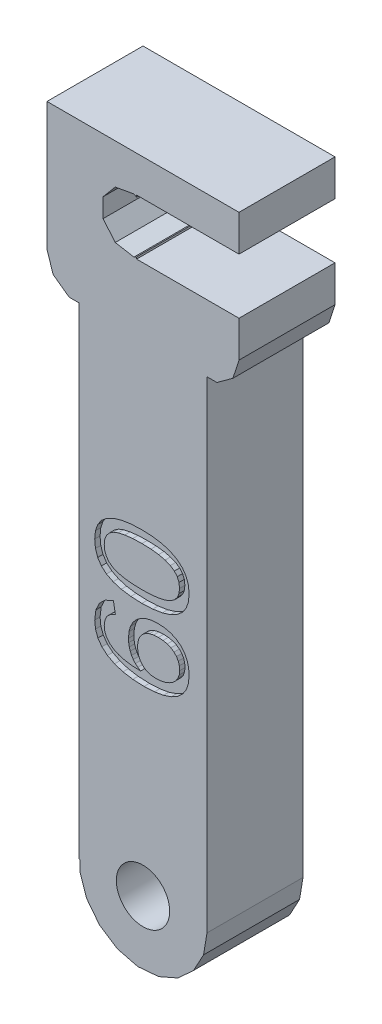
SolidWorks part; units mm, degrees
ref_plane "Front Plane" through (0, 0, 0) normal (0, 0, 1) x (1, 0, 0)
ref_plane "Top Plane" through (0, 0, 0) normal (0, 1, 0) x (1, 0, 0)
ref_plane "Right Plane" through (0, 0, 0) normal (1, 0, 0) x (0, 0, -1)
ref_plane "Plane1" through (0, 0, 4.5) normal (0, 0, 1) x (1, 0, 0)
sketch "Sketch1" plane through (0, 0, 4.5) normal (0, 0, 1) x (1, 0, 0)
  line L0 (8.427, 16.2366) -> (9, 18)
  line L1 (9, 18) -> (9, 30)
  line L2 (9, 30) -> (-9, 30)
  line L3 (-9, 30) -> (-9, 18)
  line L4 (-9, 18) -> (-8.427, 16.2366)
  line L5 (-8.427, 16.2366) -> (-6.9271, 15.1468)
  line L6 (-6.9271, 15.1468) -> (-6, 15.1468)
  line L7 (-6, 15.1468) -> (-6, -30)
  line L8 (-6, -30) -> (-5.9182, -30)
  line L9 (-5.9182, -30) -> (-5.9182, -30.9876)
  line L10 (-5.9182, -30.9876) -> (-5.2768, -32.8557)
  line L11 (-5.2768, -32.8557) -> (-4.0637, -34.4143)
  line L12 (-4.0637, -34.4143) -> (-2.4102, -35.4946)
  line L13 (-2.4102, -35.4946) -> (-0.4955, -35.9795)
  line L14 (-0.4955, -35.9795) -> (1.4729, -35.8164)
  line L15 (1.4729, -35.8164) -> (3.2817, -35.023)
  line L16 (3.2817, -35.023) -> (4.7348, -33.6853)
  line L17 (4.7348, -33.6853) -> (5.6749, -31.9482)
  line L18 (5.6749, -31.9482) -> (6, -30)
  line L19 (6, -30) -> (6, 15.1468)
  line L20 (6, 15.1468) -> (6.9271, 15.1468)
  line L21 (6.9271, 15.1468) -> (8.427, 16.2366)
extrude "Boss-Extrude1" add sketch "Sketch1" against normal blind 9
sketch "Sketch2" plane through (0, 0, -4.5) normal (0, 0, -1) x (-1, 0, 0)
  line L0 (-9, 26.6) -> (-9, 21.4)
  line L1 (-9, 21.4) -> (0.6, 21.4)
  line L2 (0.6, 21.4) -> (0.6, 21.583)
  line L3 (0.6, 21.583) -> (0.8485, 21.4395)
  line L4 (0.8485, 21.4395) -> (2.6, 21.7483)
  line L5 (2.6, 21.7483) -> (3.7432, 23.1107)
  line L6 (3.7432, 23.1107) -> (3.7432, 24.8893)
  line L7 (3.7432, 24.8893) -> (2.6, 26.2517)
  line L8 (2.6, 26.2517) -> (1.6624, 26.417)
  line L9 (1.6624, 26.417) -> (0.6, 26.417)
  line L10 (0.6, 26.417) -> (0.6, 26.6)
  line L11 (0.6, 26.6) -> (-9, 26.6)
extrude "Cut-Extrude1" cut sketch "Sketch2" against normal through all
sketch "Sketch3" plane through (0, 0, -4.5) normal (0, 0, -1) x (-1, 0, 0)
  line L0 (1.7678, -28.2322) -> (0, -27.5)
  line L1 (0, -27.5) -> (-1.7678, -28.2322)
  line L2 (-1.7678, -28.2322) -> (-2.5, -30)
  line L3 (-2.5, -30) -> (-1.7678, -31.7678)
  line L4 (-1.7678, -31.7678) -> (0, -32.5)
  line L5 (0, -32.5) -> (1.7678, -31.7678)
  line L6 (1.7678, -31.7678) -> (2.5, -30)
  line L7 (2.5, -30) -> (1.7678, -28.2322)
extrude "Cut-Extrude2" cut sketch "Sketch3" against normal through all
sketch "Sketch4" plane through (0, 0, 4.5) normal (0, 0, 1) x (1, 0, 0)
  line L0 (-2.5848, -8.4634) -> (-2.774, -7.4137)
  line L1 (-2.774, -7.4137) -> (-3.5403, -7.757)
  line L2 (-3.5403, -7.757) -> (-4.0877, -8.2803)
  line L3 (-4.0877, -8.2803) -> (-4.4161, -8.9837)
  line L4 (-4.4161, -8.9837) -> (-4.5256, -9.8672)
  line L5 (-4.5256, -9.8672) -> (-4.4508, -10.5633)
  line L6 (-4.4508, -10.5633) -> (-4.2265, -11.1748)
  line L7 (-4.2265, -11.1748) -> (-3.8527, -11.7015)
  line L8 (-3.8527, -11.7015) -> (-3.3293, -12.1436)
  line L9 (-3.3293, -12.1436) -> (-2.6664, -12.4934)
  line L10 (-2.6664, -12.4934) -> (-1.8738, -12.7432)
  line L11 (-1.8738, -12.7432) -> (-0.9514, -12.8931)
  line L12 (-0.9514, -12.8931) -> (0.1006, -12.9431)
  line L13 (0.1006, -12.9431) -> (1.0706, -12.895)
  line L14 (1.0706, -12.895) -> (1.9178, -12.7509)
  line L15 (1.9178, -12.7509) -> (2.6422, -12.5106)
  line L16 (2.6422, -12.5106) -> (3.2437, -12.1741)
  line L17 (3.2437, -12.1741) -> (3.7163, -11.7469)
  line L18 (3.7163, -11.7469) -> (4.0539, -11.2343)
  line L19 (4.0539, -11.2343) -> (4.2564, -10.6361)
  line L20 (4.2564, -10.6361) -> (4.3239, -9.9526)
  line L21 (4.3239, -9.9526) -> (4.2747, -9.3377)
  line L22 (4.2747, -9.3377) -> (4.1271, -8.793)
  line L23 (4.1271, -8.793) -> (3.8811, -8.3185)
  line L24 (3.8811, -8.3185) -> (3.5367, -7.9142)
  line L25 (3.5367, -7.9142) -> (3.1072, -7.5911)
  line L26 (3.1072, -7.5911) -> (2.6059, -7.3603)
  line L27 (2.6059, -7.3603) -> (2.033, -7.2219)
  line L28 (2.033, -7.2219) -> (1.3883, -7.1757)
  line L29 (1.3883, -7.1757) -> (0.7917, -7.2194)
  line L30 (0.7917, -7.2194) -> (0.2592, -7.3504)
  line L31 (0.2592, -7.3504) -> (-0.2092, -7.5688)
  line L32 (-0.2092, -7.5688) -> (-0.6135, -7.8746)
  line L33 (-0.6135, -7.8746) -> (-0.9392, -8.2547)
  line L34 (-0.9392, -8.2547) -> (-1.1719, -8.6962)
  line L35 (-1.1719, -8.6962) -> (-1.3115, -9.1991)
  line L36 (-1.3115, -9.1991) -> (-1.3581, -9.7634)
  line L37 (-1.3581, -9.7634) -> (-1.3399, -10.1044)
  line L38 (-1.3399, -10.1044) -> (-1.2856, -10.4256)
  line L39 (-1.2856, -10.4256) -> (-1.195, -10.727)
  line L40 (-1.195, -10.727) -> (-1.0682, -11.0085)
  line L41 (-1.0682, -11.0085) -> (-0.9066, -11.2648)
  line L42 (-0.9066, -11.2648) -> (-0.7119, -11.4906)
  line L43 (-0.7119, -11.4906) -> (-0.484, -11.6859)
  line L44 (-0.484, -11.6859) -> (-0.2229, -11.8507)
  line L45 (-0.2229, -11.8507) -> (-1.0039, -11.8184)
  line L46 (-1.0039, -11.8184) -> (-1.6869, -11.7218)
  line L47 (-1.6869, -11.7218) -> (-2.2718, -11.5606)
  line L48 (-2.2718, -11.5606) -> (-2.7587, -11.335)
  line L49 (-2.7587, -11.335) -> (-3.1419, -11.0506)
  line L50 (-3.1419, -11.0506) -> (-3.4156, -10.7132)
  line L51 (-3.4156, -10.7132) -> (-3.5798, -10.3228)
  line L52 (-3.5798, -10.3228) -> (-3.6345, -9.8794)
  line L53 (-3.6345, -9.8794) -> (-3.5689, -9.3812)
  line L54 (-3.5689, -9.3812) -> (-3.3721, -8.9792)
  line L55 (-3.3721, -8.9792) -> (-3.0441, -8.6732)
  line L56 (-3.0441, -8.6732) -> (-2.5848, -8.4634)
extrude "Cut-Extrude3" cut sketch "Sketch4" against normal blind 0.5
sketch "Sketch5" plane through (0, 0, 4) normal (0, 0, 1) x (1, 0, 0)
  line L0 (3.2803, -10.6888) -> (3.0819, -10.9866)
  line L1 (3.0819, -10.9866) -> (2.8043, -11.2496)
  line L2 (2.8043, -11.2496) -> (2.4644, -11.4645)
  line L3 (2.4644, -11.4645) -> (2.0795, -11.618)
  line L4 (2.0795, -11.618) -> (1.6496, -11.7101)
  line L5 (1.6496, -11.7101) -> (1.1747, -11.7408)
  line L6 (1.1747, -11.7408) -> (0.8022, -11.7112)
  line L7 (0.8022, -11.7112) -> (0.4721, -11.6225)
  line L8 (0.4721, -11.6225) -> (0.1843, -11.4747)
  line L9 (0.1843, -11.4747) -> (-0.0611, -11.2678)
  line L10 (-0.0611, -11.2678) -> (-0.2574, -11.0128)
  line L11 (-0.2574, -11.0128) -> (-0.3976, -10.7208)
  line L12 (-0.3976, -10.7208) -> (-0.4817, -10.3918)
  line L13 (-0.4817, -10.3918) -> (-0.5097, -10.0258)
  line L14 (-0.5097, -10.0258) -> (-0.478, -9.6394)
  line L15 (-0.478, -9.6394) -> (-0.3831, -9.298)
  line L16 (-0.3831, -9.298) -> (-0.2247, -9.0016)
  line L17 (-0.2247, -9.0016) -> (-0.0031, -8.7503)
  line L18 (-0.0031, -8.7503) -> (0.2769, -8.55)
  line L19 (0.2769, -8.55) -> (0.6102, -8.407)
  line L20 (0.6102, -8.407) -> (0.997, -8.3211)
  line L21 (0.997, -8.3211) -> (1.4372, -8.2925)
  line L22 (1.4372, -8.2925) -> (1.8791, -8.3208)
  line L23 (1.8791, -8.3208) -> (2.271, -8.4055)
  line L24 (2.271, -8.4055) -> (2.613, -8.5466)
  line L25 (2.613, -8.5466) -> (2.905, -8.7442)
  line L26 (2.905, -8.7442) -> (3.1386, -8.9914)
  line L27 (3.1386, -8.9914) -> (3.3055, -9.2813)
  line L28 (3.3055, -9.2813) -> (3.4056, -9.6139)
  line L29 (3.4056, -9.6139) -> (3.4389, -9.9892)
  line L30 (3.4389, -9.9892) -> (3.3993, -10.3564)
  line L31 (3.3993, -10.3564) -> (3.2803, -10.6888)
extrude "Boss-Extrude2" add sketch "Sketch5" along normal blind 0.5
sketch "Sketch6" plane through (0, 0, 4.5) normal (0, 0, 1) x (1, 0, 0)
  line L0 (-1.1391, -6.2555) -> (-0.1008, -6.3007)
  line L1 (-0.1008, -6.3007) -> (0.9176, -6.2541)
  line L2 (0.9176, -6.2541) -> (1.8064, -6.1145)
  line L3 (1.8064, -6.1145) -> (2.5655, -5.8819)
  line L4 (2.5655, -5.8819) -> (3.1948, -5.5561)
  line L5 (3.1948, -5.5561) -> (3.6888, -5.1377)
  line L6 (3.6888, -5.1377) -> (4.0416, -4.6269)
  line L7 (4.0416, -4.6269) -> (4.2533, -4.0238)
  line L8 (4.2533, -4.0238) -> (4.3239, -3.3284)
  line L9 (4.3239, -3.3284) -> (4.253, -2.6321)
  line L10 (4.253, -2.6321) -> (4.0401, -2.0262)
  line L11 (4.0401, -2.0262) -> (3.6854, -1.5107)
  line L12 (3.6854, -1.5107) -> (3.1887, -1.0856)
  line L13 (3.1887, -1.0856) -> (2.5574, -0.7532)
  line L14 (2.5574, -0.7532) -> (1.7988, -0.5157)
  line L15 (1.7988, -0.5157) -> (0.9127, -0.3732)
  line L16 (0.9127, -0.3732) -> (-0.1008, -0.3258)
  line L17 (-0.1008, -0.3258) -> (-1.1292, -0.371)
  line L18 (-1.1292, -0.371) -> (-2.0233, -0.5066)
  line L19 (-2.0233, -0.5066) -> (-2.7832, -0.7326)
  line L20 (-2.7832, -0.7326) -> (-3.4087, -1.049)
  line L21 (-3.4087, -1.049) -> (-3.8973, -1.4604)
  line L22 (-3.8973, -1.4604) -> (-4.2464, -1.9713)
  line L23 (-4.2464, -1.9713) -> (-4.4558, -2.5818)
  line L24 (-4.4558, -2.5818) -> (-4.5256, -3.2918)
  line L25 (-4.5256, -3.2918) -> (-4.4566, -4.0205)
  line L26 (-4.4566, -4.0205) -> (-4.2494, -4.6444)
  line L27 (-4.2494, -4.6444) -> (-3.9042, -5.1634)
  line L28 (-3.9042, -5.1634) -> (-3.4209, -5.5774)
  line L29 (-3.4209, -5.5774) -> (-2.7992, -5.8939)
  line L30 (-2.7992, -5.8939) -> (-2.0386, -6.1199)
  line L31 (-2.0386, -6.1199) -> (-1.1391, -6.2555)
extrude "Cut-Extrude4" cut sketch "Sketch6" against normal blind 0.5
sketch "Sketch7" plane through (0, 0, 4) normal (0, 0, 1) x (1, 0, 0)
  line L0 (-2.7984, -1.8729) -> (-2.3163, -1.6846)
  line L1 (-2.3163, -1.6846) -> (-1.706, -1.5501)
  line L2 (-1.706, -1.5501) -> (-0.9675, -1.4695)
  line L3 (-0.9675, -1.4695) -> (-0.1008, -1.4426)
  line L4 (-0.1008, -1.4426) -> (0.7383, -1.4708)
  line L5 (0.7383, -1.4708) -> (1.4616, -1.5555)
  line L6 (1.4616, -1.5555) -> (2.0688, -1.6966)
  line L7 (2.0688, -1.6966) -> (2.5602, -1.8942)
  line L8 (2.5602, -1.8942) -> (2.9393, -2.1524)
  line L9 (2.9393, -2.1524) -> (3.2101, -2.4755)
  line L10 (3.2101, -2.4755) -> (3.3726, -2.8635)
  line L11 (3.3726, -2.8635) -> (3.4268, -3.3163)
  line L12 (3.4268, -3.3163) -> (3.3738, -3.7715)
  line L13 (3.3738, -3.7715) -> (3.2147, -4.1608)
  line L14 (3.2147, -4.1608) -> (2.9496, -4.484)
  line L15 (2.9496, -4.484) -> (2.5784, -4.7413)
  line L16 (2.5784, -4.7413) -> (2.0929, -4.9376)
  line L17 (2.0929, -4.9376) -> (1.4844, -5.0778)
  line L18 (1.4844, -5.0778) -> (0.7532, -5.1619)
  line L19 (0.7532, -5.1619) -> (-0.1008, -5.1899)
  line L20 (-0.1008, -5.1899) -> (-0.9774, -5.1622)
  line L21 (-0.9774, -5.1622) -> (-1.7212, -5.0793)
  line L22 (-1.7212, -5.0793) -> (-2.3322, -4.941)
  line L23 (-2.3322, -4.941) -> (-2.8106, -4.7474)
  line L24 (-2.8106, -4.7474) -> (-3.171, -4.4905)
  line L25 (-3.171, -4.4905) -> (-3.4285, -4.1623)
  line L26 (-3.4285, -4.1623) -> (-3.583, -3.7627)
  line L27 (-3.583, -3.7627) -> (-3.6345, -3.2918)
  line L28 (-3.6345, -3.2918) -> (-3.5822, -2.8324)
  line L29 (-3.5822, -2.8324) -> (-3.4255, -2.4427)
  line L30 (-3.4255, -2.4427) -> (-3.1642, -2.1229)
  line L31 (-3.1642, -2.1229) -> (-2.7984, -1.8729)
extrude "Boss-Extrude3" add sketch "Sketch7" along normal blind 0.5
draft "Draft1" type of draft neutral plane draft angle 30.003 faces to draft 1 face at (-1.1312, 26.417, 0) neutral plane through (-0.6, 26.417, 4.5) neutral plane normal (1, 0, 0) reverse direction yes parameters "D1"=30.003
sketch "Sketch8" plane through (0, 0, 4.5) normal (0, 0, 1) x (1, 0, 0)
  circle A0 centre (0, -30) radius 2.5
extrude "Cut-Extrude5" cut sketch "Sketch8" along direction (0, 0, -1) on the side against the normal through all from surface at 0 starting at face at (-0.1078, -3.3152, 4.5)
